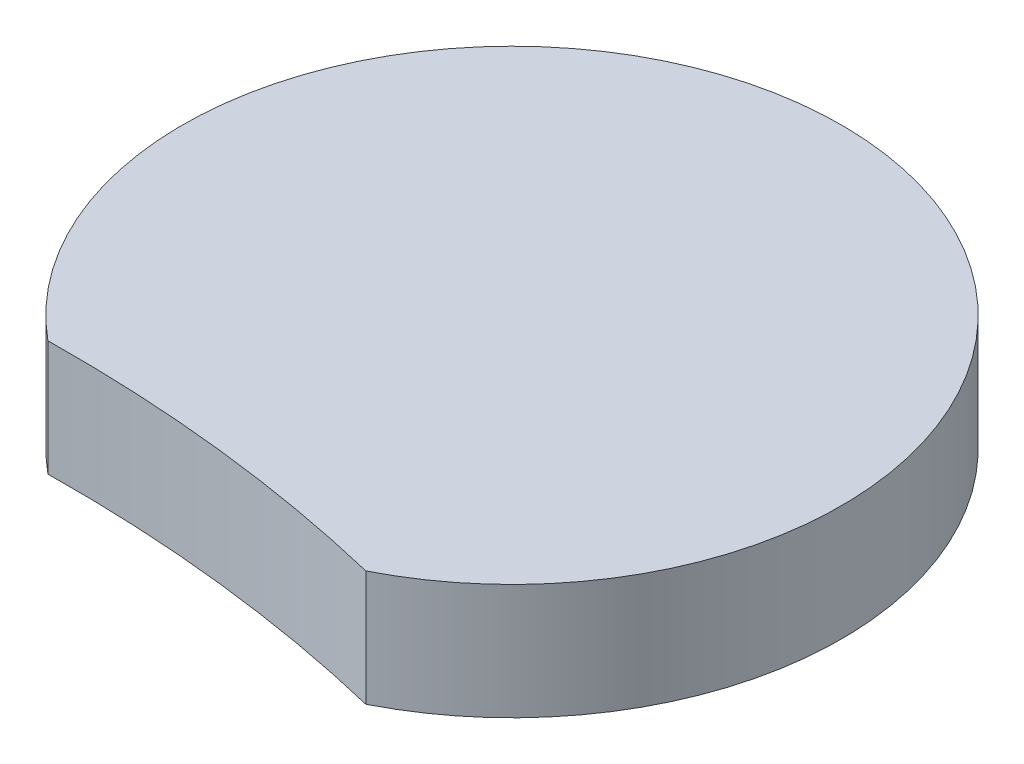
SolidWorks part; units mm, degrees
ref_plane "Front" through (0, 0, 0) normal (0, 0, 1) x (1, 0, 0)
ref_plane "Top" through (0, 0, 0) normal (0, 1, 0) x (1, 0, 0)
ref_plane "Right" through (0, 0, 0) normal (1, 0, 0) x (0, 0, -1)
sketch "Sketch1" plane through (0, 0, 0) normal (0, 1, 0) x (1, 0, 0)
  circle A0 centre (-0.0078, -0.1248) radius 5.25
  circle A1 centre (-0.0078, -0.1248) radius 13.7
  arc A2 (-9.1916, -10.6916) -> (-65.6386, -87.1835) centre (-7.9533, -70.6788) ccw construction
  arc A3 (-9.1916, -10.6916) -> (-65.6386, -87.1835) centre (-7.9533, -70.6788) ccw
  circle A4 centre (-7.9533, -70.6788) radius 60
  dimension "D1" = 10.5
extrude "Boss-Extrude1" add sketch "Sketch1" along normal blind 2.5 contours A4 A1 A0
sketch "Sketch2" plane through (0, 2.5, 0) normal (0, 1, 0) x (1, 0, 0)
  arc A5 (6.1541, -12.3608) -> (-8.7367, -10.6839) centre (-7.9533, -70.6788) ccw
  arc A6 (6.1541, -12.3608) -> (-8.7367, -10.6839) centre (-0.0078, -0.1248) ccw
  arc A7 (6.1541, -12.3608) -> (-8.7367, -10.6839) centre (-7.9533, -70.6788) ccw
  arc A8 (6.1541, -12.3608) -> (-8.7367, -10.6839) centre (-0.0078, -0.1248) ccw
  dimension "D1" = 0
extrude "Boss-Extrude2" add sketch "Sketch2" along normal blind 2.3 contours A7 A8
